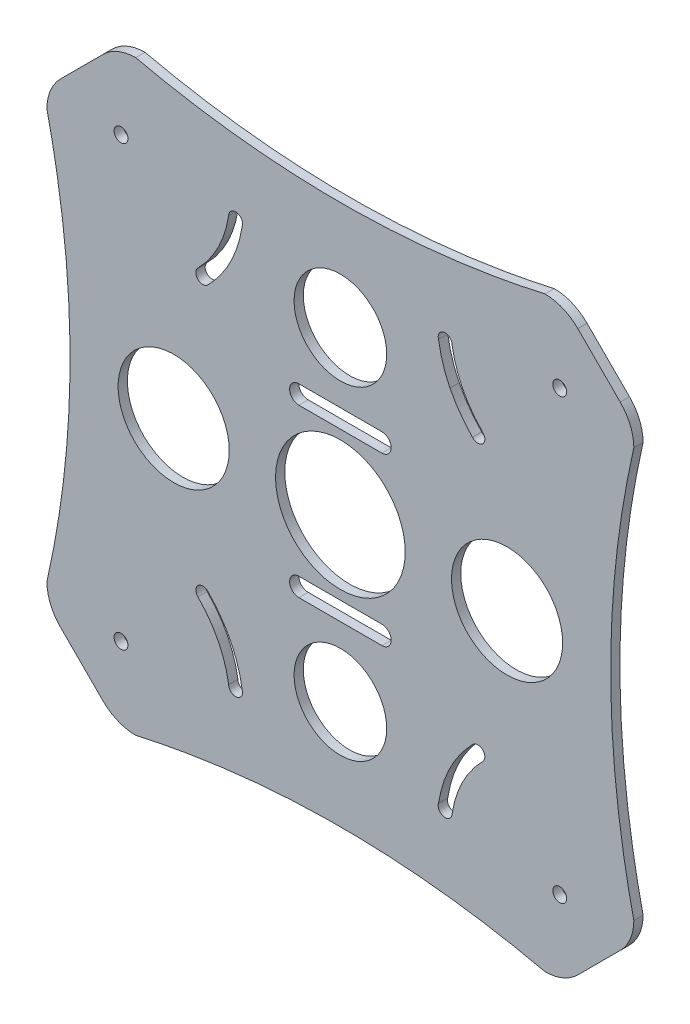
SolidWorks part; units mm, degrees
material "Hexcel AS4C (3000 Filaments)"
ref_plane "Front Plane" through (0, 0, 0) normal (0, 0, 1) x (1, 0, 0)
ref_plane "Top Plane" through (0, 0, 0) normal (0, 1, 0) x (1, 0, 0)
ref_plane "Right Plane" through (0, 0, 0) normal (1, 0, 0) x (0, 0, -1)
sketch "Sketch1" plane through (0, 0, 0) normal (0, 0, 1) x (1, 0, 0)
  line L1 (47.3762, 47.3762) -> (47.3762, 0) construction
  line L2 (47.3762, 0) -> (47.3762, -47.3762) construction
  line L3 (0, 0) -> (59.397, 59.397) construction
  line L4 (22.6274, 43.8406) -> (25.8154, 37.4647) construction
  line L5 (26.163, 36.7696) -> (16.7377, 32.0569) construction
  line L6 (26.5105, 36.0744) -> (29.6985, 29.6985) construction
  line L7 (0, 0) -> (0, -74.2241) construction
  line L8 (0, -74.2241) -> (0, 77.8962) construction
  line L9 (51.2756, 60.4472) -> (60.4472, 51.2756)
  line L10 (60.4472, -51.2756) -> (51.2756, -60.4472)
  line L11 (-51.2756, -60.4472) -> (-60.4472, -51.2756)
  line L12 (-60.4472, 51.2756) -> (-51.2756, 60.4472)
  line L13 (51.2756, -60.4472) -> (60.4472, -51.2756)
  line L15 (63.3762, 0) -> (58.3762, 0) construction
  circle A1 centre (47.3762, 47.3762) radius 1.5
  circle A2 centre (47.3762, -47.3762) radius 1.5
  arc A4 (28.5165, 28.7749) -> (30.7591, 30.7591) centre (29.6985, 29.6985) ccw
  circle A12 centre (47.3762, -47.3762) radius 1.5
  circle A13 centre (-47.3762, -47.3762) radius 1.5
  circle A14 centre (-47.3762, 47.3762) radius 1.5
  arc A15 (22.8912, 42.364) -> (23.2982, 42.499) centre (22.6274, 43.8406) ccw
  arc A16 (26.3629, 36.8549) -> (26.3497, 36.8812) centre (25.0155, 36.1958) ccw
  arc A17 (24.1274, 43.8406) -> (21.1918, 43.4059) centre (22.6274, 43.8406) ccw
  arc A18 (23.6736, 35.5255) -> (23.6738, 35.525) centre (25.0155, 36.1958) ccw
  arc A19 (-24.1274, 43.8406) -> (-21.1918, 43.4059) centre (-22.6274, 43.8406) cw
  arc A20 (-28.5165, 28.7749) -> (-30.7591, 30.7591) centre (-29.6985, 29.6985) cw
  arc A21 (-28.5165, -28.7749) -> (-30.7591, -30.7591) centre (-29.6985, -29.6985) ccw
  arc A22 (-24.1274, -43.8406) -> (-21.1918, -43.4059) centre (-22.6274, -43.8406) ccw
  arc A23 (24.1274, -43.8406) -> (21.1918, -43.4059) centre (22.6274, -43.8406) cw
  arc A24 (28.5165, -28.7749) -> (30.7591, -30.7591) centre (29.6985, -29.6985) cw
  arc A25 (63.3762, 44.2046) -> (60.4472, 51.2756) centre (53.3762, 44.2046) ccw
  arc A26 (51.2756, 60.4472) -> (44.2046, 63.3762) centre (44.2046, 53.3762) ccw
  arc A27 (63.3762, -44.2046) -> (60.4472, -51.2756) centre (53.3762, -44.2046) cw
  arc A28 (51.2756, -60.4472) -> (44.2046, -63.3762) centre (44.2046, -53.3762) cw
  arc A29 (60.4472, -51.2756) -> (63.3762, -44.2046) centre (53.3762, -44.2046) ccw
  arc A30 (44.2046, -63.3762) -> (51.2756, -60.4472) centre (44.2046, -53.3762) ccw
  arc A31 (-51.2756, -60.4472) -> (-44.2046, -63.3762) centre (-44.2046, -53.3762) ccw
  arc A32 (-63.3762, -44.2046) -> (-60.4472, -51.2756) centre (-53.3762, -44.2046) ccw
  arc A33 (-60.4472, 51.2756) -> (-63.3762, 44.2046) centre (-53.3762, 44.2046) ccw
  arc A34 (-44.2046, 63.3762) -> (-51.2756, 60.4472) centre (-44.2046, 53.3762) ccw
  spline S0 degree 2 poles (-24.1274, 43.8406) (-25.3624, 36.2517) (-30.7591, 30.7591) knots 0 0 0 1 1 1
  spline S1 degree 2 poles (24.1274, 43.8406) (25.3624, 36.2517) (30.7591, 30.7591) knots 0 0 0 1 1 1
  spline S2 degree 2 poles (21.1274, 43.8406) (22.3834, 34.9061) (28.761, 28.5275) knots 0 0 0 1 1 1
  spline S3 degree 2 poles (-21.1274, 43.8406) (-22.3834, 34.9061) (-28.761, 28.5275) knots 0 0 0 1 1 1
  spline S4 degree 2 poles (-24.1274, -43.8406) (-25.3624, -36.2517) (-30.7591, -30.7591) knots 0 0 0 1 1 1
  spline S5 degree 2 poles (-21.1274, -43.8406) (-22.3834, -34.9061) (-28.761, -28.5275) knots 0 0 0 1 1 1
  spline S6 degree 2 poles (24.1274, -43.8406) (25.3624, -36.2517) (30.7591, -30.7591) knots 0 0 0 1 1 1
  spline S7 degree 2 poles (21.1274, -43.8406) (22.3834, -34.9061) (28.761, -28.5275) knots 0 0 0 1 1 1
  spline S8 degree 2 poles (63.3762, 44.2046) (53.3762, 0) (63.3762, -44.2046) knots 0 0 0 1 1 1
  spline S9 degree 2 poles (44.2046, -63.3762) (0, -53.3762) (-44.2046, -63.3762) knots 0 0 0 1 1 1
  spline S10 degree 2 poles (-63.3762, -44.2046) (-53.3762, 0) (-63.3762, 44.2046) knots 0 0 0 1 1 1
  spline S11 degree 2 poles (-44.2046, 63.3762) (0, 53.3762) (44.2046, 63.3762) knots 0 0 0 1 1 1
  point P31 (0, 0)
  point P38 (0, 0)
  point P93 (63.3762, 48.3467)
  point P96 (48.3467, 63.3762)
  point P125 (0, 0)
  point P134 (0, 0)
  dimension "D1" = 25
  dimension "D2" = 3
  dimension "D11" = 12
  dimension "D12" = 16
  dimension "D14" = 10
  dimension "D15" = 10
  dimension "D9" = 25
  dimension "D10" = 25
  dimension "D13" = 16
  dimension "D16" = 5
  dimension "D8" = 4
  dimension "D17" = 4
extrude "Boss-Extrude1" add sketch "Sketch1" along normal blind 2
sketch "Sketch4" plane through (0, 0, 0) normal (0, 0, -1) x (-1, 0, 0)
  line L0 (0, 0) -> (-162.1255, 0) construction
  line L4 (0, 0) -> (0, 40.8652) construction
  line L5 (-8.9657, 18) -> (8.9657, 18) construction
  line L6 (-8.9657, 20) -> (8.9657, 20)
  line L7 (-8.9657, 16) -> (8.9657, 16)
  line L11 (8.9657, -18) -> (-8.9657, -18) construction
  line L12 (8.9657, -20) -> (-8.9657, -20)
  line L13 (8.9657, -16) -> (-8.9657, -16)
  circle A0 centre (0, 0) radius 14
  circle A1 centre (-36, 0) radius 12
  circle A2 centre (36, 0) radius 12
  circle A4 centre (0, 35) radius 10
  arc A5 (-8.9657, 20) -> (-8.9657, 16) centre (-8.9657, 18) ccw
  arc A6 (8.9657, 16) -> (8.9657, 20) centre (8.9657, 18) ccw
  circle A10 centre (0, -35) radius 10
  arc A11 (8.9657, -20) -> (8.9657, -16) centre (8.9657, -18) ccw
  arc A12 (-8.9657, -16) -> (-8.9657, -20) centre (-8.9657, -18) ccw
  point P21 (0, 18)
  point P39 (0, -18)
  point P44 (0, 0)
  dimension "D1" = 36
extrude "Cut-Extrude1" cut sketch "Sketch4" against normal blind 10
